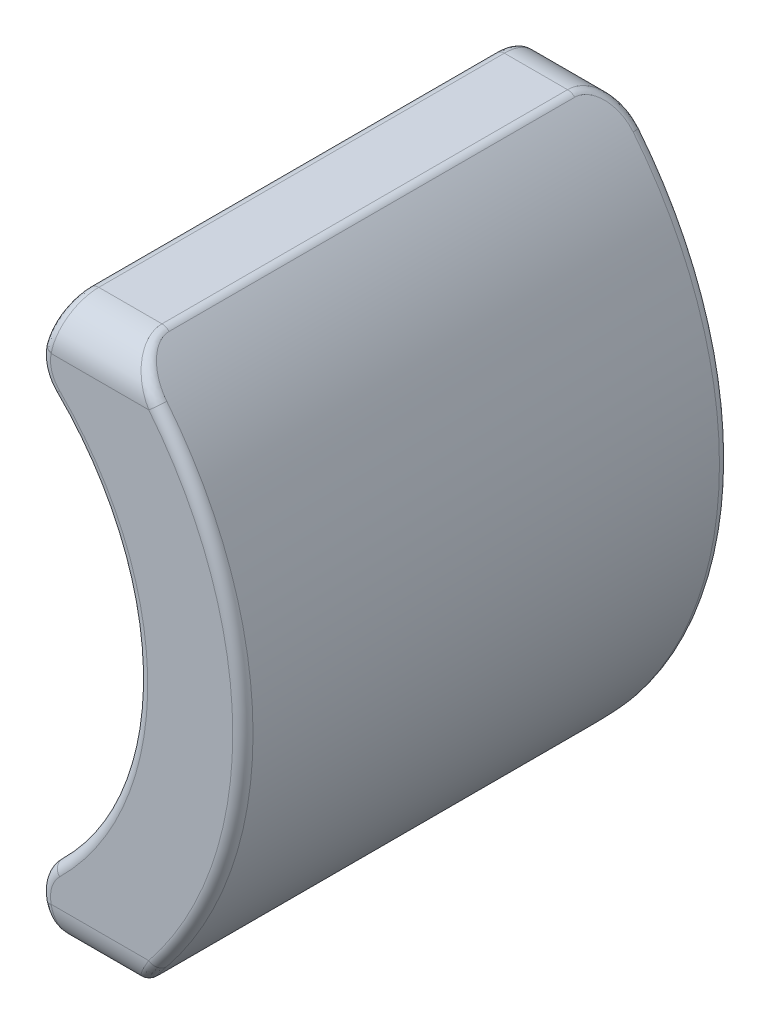
SolidWorks part; units mm, degrees
ref_plane "Front Plane" through (0, 0, 0) normal (0, 0, 1) x (1, 0, 0)
ref_plane "Top Plane" through (0, 0, 0) normal (0, 1, 0) x (1, 0, 0)
ref_plane "Right Plane" through (0, 0, 0) normal (1, 0, 0) x (0, 0, -1)
sketch "Sketch1" plane through (0, 0, 0) normal (0, 0, 1) x (1, 0, 0)
  line L0 (0, 0) -> (9.63, 0) construction
  line L1 (6.7381, -6.88) -> (4.8781, -6.88)
  line L2 (4.8781, -6.88) -> (4.5318, -5.38)
  line L3 (4.8781, 6.88) -> (4.5318, 5.38)
  line L4 (6.7381, 6.88) -> (4.8781, 6.88)
  arc A0 (6.7381, 6.88) -> (6.7381, -6.88) centre (0, 0) cw
  arc A1 (4.5318, 5.38) -> (4.5318, -5.38) centre (0, 0) cw
  point P7 (9.63, 0)
  dimension "D1" = 9.63
  dimension "D2" = 6.88
  dimension "D3" = 103
  dimension "D4" = 1.86
  dimension "D5" = 1.5
extrude "Boss-Extrude1" add sketch "Sketch1" along normal blind 12
fillet "Fillet1" radius 1 2 edges at (4.5318, 5.38, 6) (4.5318, -5.38, 6)
fillet "Fillet2" radius 1 4 edges at (5.8081, -6.88, 0) (5.8081, -6.88, 12) (5.8081, 6.88, 12) (5.8081, 6.88, 0)
fillet "Fillet3" radius 0.25 24 edges at (4.8161, -6.6112, 0.3178) (4.8781, -6.88, 6) (4.8161, -6.6112, 11.6822) (4.6879, -5.4113, 12) (7.0343, 0, 12) (4.6879, 5.4113, 12) (4.8161, 6.6112, 11.6822) (4.8781, 6.88, 6) (4.8161, 6.6112, 0.3178) (6.8685, -6.7498, 0.5066) (6.7381, -6.88, 6) (6.9882, -6.6258, 11.6661) (9.63, 0, 12) (6.8685, 6.7498, 11.4934) (6.7381, 6.88, 6) (6.9882, 6.6258, 0.3339) (4.6879, 5.4113, 0) (7.0343, 0, 0) (4.6879, -5.4113, 0) (9.63, 0, 0)
